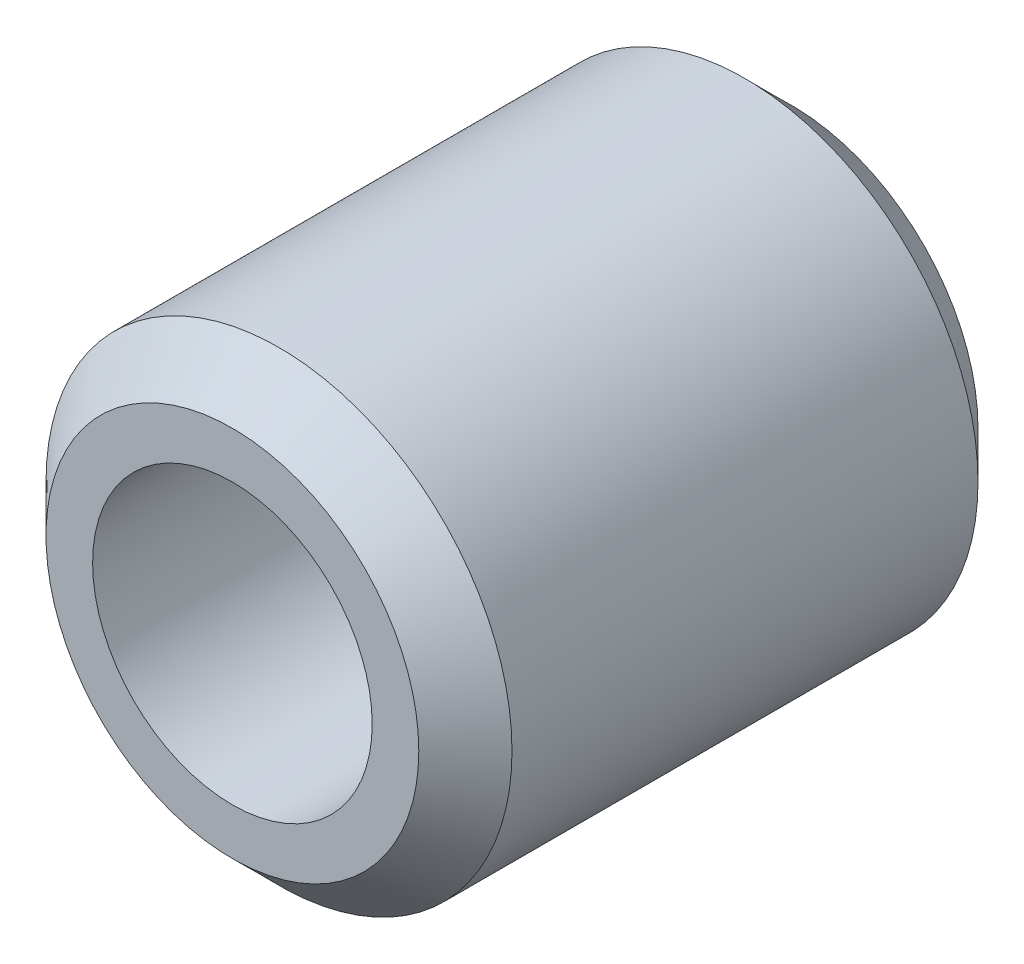
SolidWorks part; units mm, degrees
material "Alloy Steel"
ref_plane "Front Plane" through (0, 0, 0) normal (0, 0, 1) x (1, 0, 0)
ref_plane "Top Plane" through (0, 0, 0) normal (0, 1, 0) x (1, 0, 0)
ref_plane "Right Plane" through (0, 0, 0) normal (1, 0, 0) x (0, 0, -1)
sketch "Sketch1" plane through (0, 0, 0) normal (0, 0, 1) x (1, 0, 0)
  circle A0 centre (0, 0) radius 7.9375
  dimension "D1" = 15.875
extrude "Boss-Extrude1" add sketch "Sketch1" along normal blind 19.05
sketch "Sketch2" plane through (0, 0, 19.05) normal (0, 0, 1) x (1, 0, 0)
  circle A0 centre (0, 0) radius 4.7625
  dimension "D1" = 9.525
extrude "Cut-Extrude1" cut sketch "Sketch2" against normal blind 12.7
chamfer "Chamfer1" distance 1.5875 angle 45 2 edges at (7.9375, 0, 0) (7.9375, 0, 19.05)
